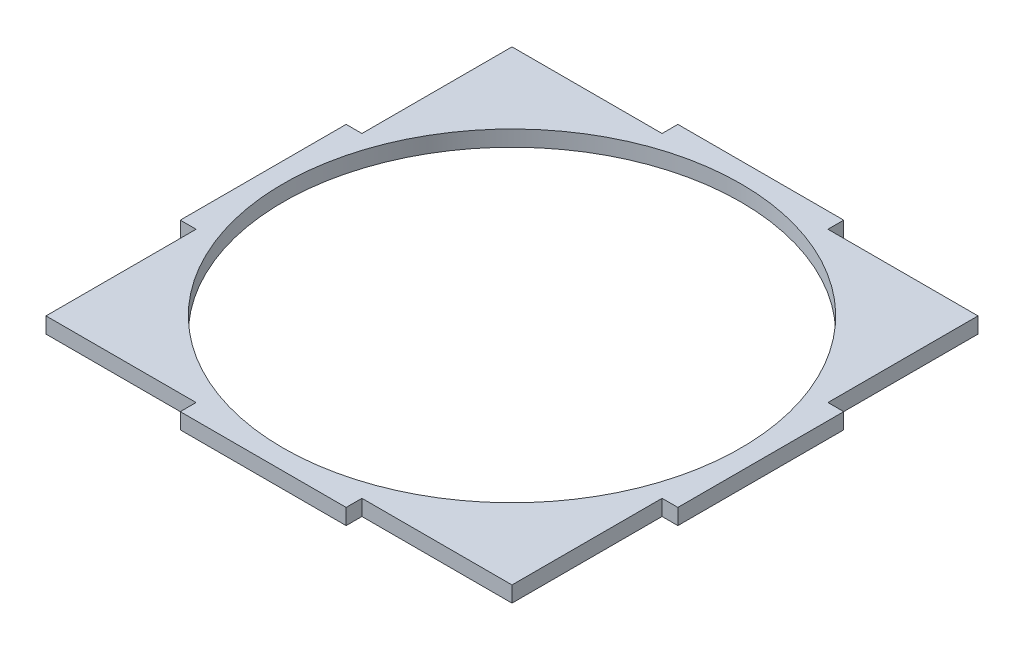
SolidWorks part; units mm, degrees
ref_plane "Front Plane" through (0, 0, 0) normal (0, 0, 1) x (1, 0, 0)
ref_plane "Top Plane" through (0, 0, 0) normal (0, 1, 0) x (1, 0, 0)
ref_plane "Right Plane" through (0, 0, 0) normal (1, 0, 0) x (0, 0, -1)
sketch "Sketch2" plane through (0, 0, 0) normal (0, 1, 0) x (1, 0, 0)
  line L0 (-50, -16.6667) -> (-50, 16.6667)
  line L1 (-16.6667, -50) -> (16.6667, -50)
  line L3 (-16.6667, 50) -> (16.6667, 50)
  line L4 (50, -16.6667) -> (50, 16.6667)
  line L5 (-50, -50) -> (50, 50) construction
  line L6 (-50, 50) -> (50, -50) construction
  line L7 (-50, -16.6667) -> (-46.825, -16.6667)
  line L10 (-46.825, -16.6667) -> (-46.825, -46.825)
  line L13 (-46.825, -46.825) -> (-16.6667, -46.825)
  line L14 (-16.6667, -50) -> (-16.6667, -46.825)
  line L15 (0, 50) -> (0, -50) construction
  line L17 (-16.6667, 50) -> (-16.6667, 46.825)
  line L18 (-16.6667, 46.825) -> (-46.825, 46.825)
  line L22 (-50, 16.6667) -> (-46.825, 16.6667)
  line L23 (-46.825, 46.825) -> (-46.825, 16.6667)
  line L24 (16.6667, -50) -> (16.6667, -46.825)
  line L25 (46.825, -46.825) -> (16.6667, -46.825)
  line L26 (46.825, -16.6667) -> (46.825, -46.825)
  line L27 (50, -16.6667) -> (46.825, -16.6667)
  line L28 (50, 16.6667) -> (46.825, 16.6667)
  line L29 (46.825, 46.825) -> (46.825, 16.6667)
  line L30 (16.6667, 46.825) -> (46.825, 46.825)
  line L31 (16.6667, 50) -> (16.6667, 46.825)
  circle A0 centre (0, 0) radius 45 construction
  circle A1 centre (0, 0) radius 46
  dimension "D1" = 90
  dimension "D4" = 92
  dimension "D2" = 100
  dimension "D3" = 100
  dimension "D5" = 3.175
  dimension "D7" = 3.175
  dimension "D8" = 33.3333
  dimension "D6" = 33.3333
  dimension "D9" = 3.175
  dimension "D10" = 33.3333
  dimension "D11" = 3.175
  dimension "D12" = 33.3333
extrude "Boss-Extrude1" add sketch "Sketch2" along normal blind 3.175
equation "\"spinner diameter\"=9"
equation "\"D1@Sketch2\"=\"spinner diameter\""
equation "\"BaseLength\"=10"
equation "\"D2@Sketch2\"=\"BaseLength\""
equation "\"D3@Sketch2\"=\"BaseLength\""
equation "\"D4@Sketch2\"=\"spinner diameter\"+0.2"
